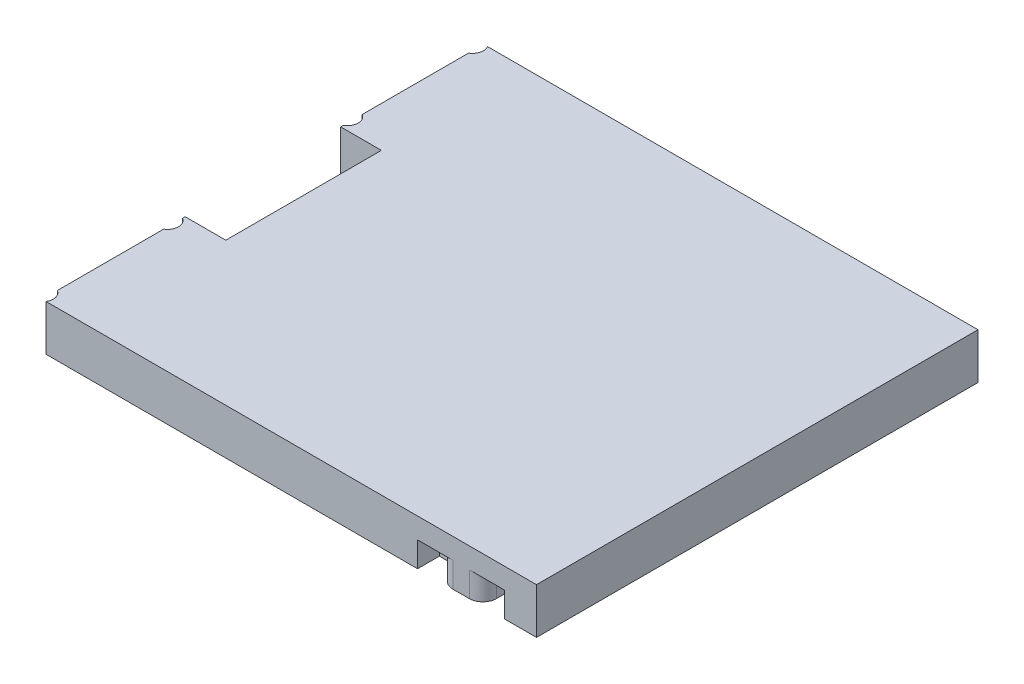
SolidWorks part; units mm, degrees
ref_plane "Front Plane" through (0, 0, 0) normal (0, 0, 1) x (1, 0, 0)
ref_plane "Top Plane" through (0, 0, 0) normal (0, 1, 0) x (1, 0, 0)
ref_plane "Right Plane" through (0, 0, 0) normal (1, 0, 0) x (0, 0, -1)
sketch "Sketch1" plane through (0, 0, 0) normal (0, 1, 0) x (1, 0, 0)
  line L1 (-46.1, 40.55) -> (46.1, 40.55)
  line L2 (-46.1, 40.55) -> (-46.1, -40.55)
  line L3 (-46.1, -40.55) -> (46.1, -40.55)
  line L4 (46.1, 40.55) -> (46.1, -40.55)
  line L5 (-46.1, 40.55) -> (46.1, -40.55) construction
  line L6 (-46.1, -40.55) -> (46.1, 40.55) construction
  point P0 (0, 0)
  dimension "D1" = 92.2
  dimension "D2" = 81.1
extrude "Boss-Extrude1" add sketch "Sketch1" along normal mid plane 8.4 contours L2 L3 L4 L1
sketch "Sketch2" plane through (0, -4.2, 0) normal (0, -1, 0) x (1, 0, 0)
  line L0 (38.85, 40.55) -> (34.85, 40.55) construction
  line L1 (38.85, 36.55) -> (38.85, 40.55) construction
  line L2 (34.85, 36.55) -> (38.85, 36.55) construction
  line L3 (34.85, 40.55) -> (34.85, 36.55) construction
  line L4 (38.85, 40.55) -> (34.85, 40.55)
  line L5 (38.85, 36.55) -> (38.85, 40.55)
  line L6 (34.85, 36.55) -> (38.85, 36.55)
  line L7 (34.85, 38.05) -> (34.85, 36.55)
  line L8 (22.85, 36.55) -> (26.85, 36.55) construction
  line L9 (26.85, 36.55) -> (26.85, 40.55) construction
  line L10 (22.85, 40.55) -> (22.85, 36.55) construction
  line L11 (26.85, 40.55) -> (22.85, 40.55) construction
  line L12 (22.85, 36.55) -> (26.85, 36.55)
  line L13 (26.85, 36.55) -> (26.85, 38.05)
  line L14 (22.85, 40.55) -> (22.85, 36.55)
  line L15 (26.85, 40.55) -> (22.85, 40.55)
  line L18 (22.85, -36.55) -> (22.85, -40.55) construction
  line L19 (26.85, -36.55) -> (22.85, -36.55) construction
  line L20 (26.85, -38.05) -> (26.85, -36.55) construction
  line L22 (34.85, -36.55) -> (34.85, -38.05) construction
  line L23 (38.85, -36.55) -> (34.85, -36.55) construction
  line L24 (38.85, -40.55) -> (38.85, -36.55) construction
  line L25 (22.85, -36.55) -> (22.85, -40.55)
  line L26 (26.85, -36.55) -> (22.85, -36.55)
  line L27 (26.85, -38.05) -> (26.85, -36.55)
  line L29 (34.85, -36.55) -> (34.85, -38.05)
  line L30 (38.85, -36.55) -> (34.85, -36.55)
  line L31 (38.85, -40.55) -> (38.85, -36.55)
  line L32 (22.85, -40.55) -> (29.35, -40.55)
  line L33 (26.85, 40.55) -> (29.35, 40.55)
  line L34 (32.35, 40.55) -> (34.85, 40.55)
  line L35 (32.35, -40.55) -> (38.85, -40.55)
  arc A1 (29.35, 40.55) -> (26.85, 38.05) centre (29.35, 38.05) ccw construction
  arc A2 (34.85, 38.05) -> (32.35, 40.55) centre (32.35, 38.05) ccw construction
  arc A3 (29.35, 40.55) -> (26.85, 38.05) centre (29.35, 38.05) ccw
  arc A4 (34.85, 38.05) -> (32.35, 40.55) centre (32.35, 38.05) ccw
  arc A5 (26.85, -38.05) -> (29.35, -40.55) centre (29.35, -38.05) ccw construction
  arc A6 (32.35, -40.55) -> (34.85, -38.05) centre (32.35, -38.05) ccw construction
  arc A7 (26.85, -38.05) -> (29.35, -40.55) centre (29.35, -38.05) ccw
  arc A8 (32.35, -40.55) -> (34.85, -38.05) centre (32.35, -38.05) ccw
extrude "Cut-Extrude1" cut sketch "Sketch2" against normal blind 4.6
sketch "Sketch3" plane through (0, -4.2, 0) normal (0, -1, 0) x (1, 0, 0)
  line L1 (38.85, 40.55) -> (46.1, 40.55) construction
  line L2 (-46.1, 40.55) -> (22.85, 40.55) construction
  line L5 (46.1, -40.55) -> (46.1, 40.55) construction
  line L6 (45, 40.55) -> (46.1, 40.55)
  line L7 (46.1, 40.55) -> (46.1, 34.4)
  line L8 (46.1, -34.4) -> (46.1, -40.55)
  line L9 (46.1, -40.55) -> (45, -40.55)
  line L10 (38.85, -40.55) -> (46.1, -40.55) construction
  line L11 (-46.1, -37.7679) -> (-46.1, -40.55)
  line L12 (-46.1, -40.55) -> (-45.3978, -40.55)
  line L13 (-46.1, -40.55) -> (22.85, -40.55) construction
  line L14 (-46.1, -14.7679) -> (-46.1, -18.2321)
  line L15 (-46.1, 18.2321) -> (-46.1, 14.7679)
  line L16 (-45.3978, 40.55) -> (-46.1, 40.55)
  line L17 (-46.1, 40.55) -> (-46.1, 37.7679)
  line L26 (21.2, -33.9) -> (21.2, -49.9)
  line L27 (21.2, -49.9) -> (39.6, -49.9)
  line L28 (40.1, -49.4) -> (40.1, -47.65)
  line L29 (40.6, -47.15) -> (44.5, -47.15)
  line L30 (45, -46.65) -> (45, -34.9)
  line L31 (45.5, -34.4) -> (48.1, -34.4)
  line L32 (48.6, -33.9) -> (48.6, 33.9)
  line L33 (48.1, 34.4) -> (45.5, 34.4)
  line L34 (45, 34.9) -> (45, 46.65)
  line L35 (44.5, 47.15) -> (40.6, 47.15)
  line L36 (40.1, 47.65) -> (40.1, 49.4)
  line L37 (39.6, 49.9) -> (21.2, 49.9)
  line L38 (21.2, 49.9) -> (21.2, 33.9)
  line L39 (19.2, 31.9) -> (-21.8, 31.9)
  line L40 (-23.8, 33.9) -> (-23.8, 49.9)
  line L41 (-23.8, 49.9) -> (-40.3, 49.9)
  line L42 (-40.3, 49.9) -> (-46.1, 44.1)
  line L43 (-46.1, 44.1) -> (-46.1, 41.2321)
  line L44 (-46.1, 37.7679) -> (-46.1, 18.2321)
  line L45 (-46.1, 14.7679) -> (-46.1, -14.7679)
  line L46 (-46.1, -18.2321) -> (-46.1, -37.7679)
  line L47 (-46.1, -41.2321) -> (-46.1, -44.1)
  line L48 (-46.1, -44.1) -> (-40.3, -49.9)
  line L49 (-40.3, -49.9) -> (-23.8, -49.9)
  line L50 (-23.8, -49.9) -> (-23.8, -33.9)
  line L51 (-21.8, -31.9) -> (19.2, -31.9)
  line L56 (45, -40.55) -> (45, -34.9)
  line L57 (45.5, -34.4) -> (46.1, -34.4)
  line L59 (46.1, 34.4) -> (45.5, 34.4)
  line L60 (45, 34.9) -> (45, 40.55)
  arc A19 (39.6, -49.9) -> (40.1, -49.4) centre (39.6, -49.4) ccw
  arc A20 (40.6, -47.15) -> (40.1, -47.65) centre (40.6, -47.65) ccw
  arc A21 (44.5, -47.15) -> (45, -46.65) centre (44.5, -46.65) ccw
  arc A22 (45.5, -34.4) -> (45, -34.9) centre (45.5, -34.9) ccw
  arc A23 (48.1, -34.4) -> (48.6, -33.9) centre (48.1, -33.9) ccw
  arc A24 (48.6, 33.9) -> (48.1, 34.4) centre (48.1, 33.9) ccw
  arc A25 (45, 34.9) -> (45.5, 34.4) centre (45.5, 34.9) ccw
  arc A26 (45, 46.65) -> (44.5, 47.15) centre (44.5, 46.65) ccw
  arc A27 (40.1, 47.65) -> (40.6, 47.15) centre (40.6, 47.65) ccw
  arc A28 (40.1, 49.4) -> (39.6, 49.9) centre (39.6, 49.4) ccw
  arc A29 (19.2, 31.9) -> (21.2, 33.9) centre (19.2, 33.9) ccw
  arc A30 (-23.8, 33.9) -> (-21.8, 31.9) centre (-21.8, 33.9) ccw
  arc A31 (-46.1, 37.7679) -> (-46.1, 41.2321) centre (-47.1, 39.5) ccw
  arc A32 (-46.1, 14.7679) -> (-46.1, 18.2321) centre (-47.1, 16.5) ccw
  arc A33 (-46.1, -18.2321) -> (-46.1, -14.7679) centre (-47.1, -16.5) ccw
  arc A34 (-46.1, -41.2321) -> (-46.1, -37.7679) centre (-47.1, -39.5) ccw
  arc A35 (-21.8, -31.9) -> (-23.8, -33.9) centre (-21.8, -33.9) ccw
  arc A36 (21.2, -33.9) -> (19.2, -31.9) centre (19.2, -33.9) ccw
  arc A40 (45.5, -34.4) -> (45, -34.9) centre (45.5, -34.9) ccw
  arc A43 (45, 34.9) -> (45.5, 34.4) centre (45.5, 34.9) ccw
  arc A49 (-46.1, 37.7679) -> (-45.3978, 40.55) centre (-47.1, 39.5) ccw
  arc A50 (-46.1, 14.7679) -> (-46.1, 18.2321) centre (-47.1, 16.5) ccw
  arc A51 (-46.1, -18.2321) -> (-46.1, -14.7679) centre (-47.1, -16.5) ccw
  arc A52 (-45.3978, -40.55) -> (-46.1, -37.7679) centre (-47.1, -39.5) ccw
  dimension "D1" = 0
extrude "Cut-Extrude2" cut sketch "Sketch3" against normal through all
sketch "Sketch4" plane through (0, -4.2, 0) normal (0, -1, 0) x (1, 0, 0)
  line L2 (-38.632, 11.8872) -> (-38.632, 12.2428) construction
  line L3 (-38.632, 11.8872) -> (-38.632, 12.2428)
  line L4 (-38.632, -12.2428) -> (-38.632, -11.8872) construction
  line L7 (-38.632, -12.2428) -> (-38.632, -11.8872)
  line L8 (-46.125, 14.2875) -> (-40.537, 14.2875) construction
  line L9 (-46.125, 14.2875) -> (-40.537, 14.2875)
  line L11 (-38.632, -11.8872) -> (-38.632, 11.8872)
  line L14 (-46.125, 14.2875) -> (-46.125, 13.6525)
  line L16 (-40.537, 13.0175) -> (-40.537, 13.6525)
  line L17 (-42.061, 13.0175) -> (-40.537, 13.0175)
  line L18 (-42.061, -13.0175) -> (-42.061, 13.0175)
  line L19 (-40.537, -13.0175) -> (-42.061, -13.0175)
  line L20 (-40.537, -14.2875) -> (-40.537, -13.0175)
  line L21 (-46.125, -14.2875) -> (-40.537, -14.2875)
  line L22 (-46.125, 13.6525) -> (-46.125, -14.2875)
  line L23 (-40.537, 13.6525) -> (-46.125, 13.6525)
  line L29 (-46.125, -14.2875) -> (-40.537, -14.2875)
  line L30 (-46.125, 13.6525) -> (-46.125, -14.2875)
  line L56 (-40.537, 14.2875) -> (-38.632, 14.2875)
  line L57 (-38.632, 14.2875) -> (-38.632, 12.2428)
  line L58 (-40.537, -14.2875) -> (-38.632, -14.2875)
  line L59 (-38.632, -14.2875) -> (-38.632, -12.2428)
  dimension "D1" = 0
extrude "Cut-Extrude3" cut sketch "Sketch4" against normal through all
sketch "Sketch5" plane through (0, -4.2, 0) normal (0, -1, 0) x (1, 0, 0)
  circle A1 centre (41.25, -25) radius 2.35 construction
  circle A2 centre (41.25, -25) radius 2.35
  circle A3 centre (41.25, 25) radius 2.35 construction
  circle A4 centre (41.25, 25) radius 2.35
  circle A5 centre (19.5, 0) radius 2.35 construction
  circle A6 centre (19.5, 0) radius 2.35
  circle A7 centre (-1.3, 15) radius 1.9 construction
  circle A8 centre (-1.3, 15) radius 1.9
  circle A9 centre (-1.3, -15) radius 1.9 construction
  circle A10 centre (-1.3, -15) radius 1.9
  circle A11 centre (-22.1, 0) radius 2.35 construction
  circle A12 centre (-22.1, 0) radius 2.35
  circle A13 centre (-43.85, -25) radius 2.35 construction
  circle A14 centre (-43.85, -25) radius 2.35
  circle A15 centre (-43.85, 25) radius 2.35 construction
  circle A16 centre (-43.85, 25) radius 2.35
extrude "Cut-Extrude4" cut sketch "Sketch5" against normal blind 1.5
sketch "Sketch6" plane through (0, -4.2, 0) normal (0, -1, 0) x (1, 0, 0)
  line L7 (44.7, 40.55) -> (46.1, 40.55)
  line L8 (38.85, 40.55) -> (45, 40.55) construction
  line L9 (44.7, 40.55) -> (44.7, -40.55)
  line L10 (38.85, -40.55) -> (45, -40.55) construction
  line L11 (44.7, -40.55) -> (46.1, -40.55)
  line L12 (46.1, -40.55) -> (46.1, 40.55)
  line L13 (45, 40.55) -> (45, 34.9) construction
  line L14 (46.1, -34.4) -> (46.1, 34.4) construction
  dimension "D1" = 0.3
extrude "Cut-Extrude5" cut sketch "Sketch6" against normal through all
